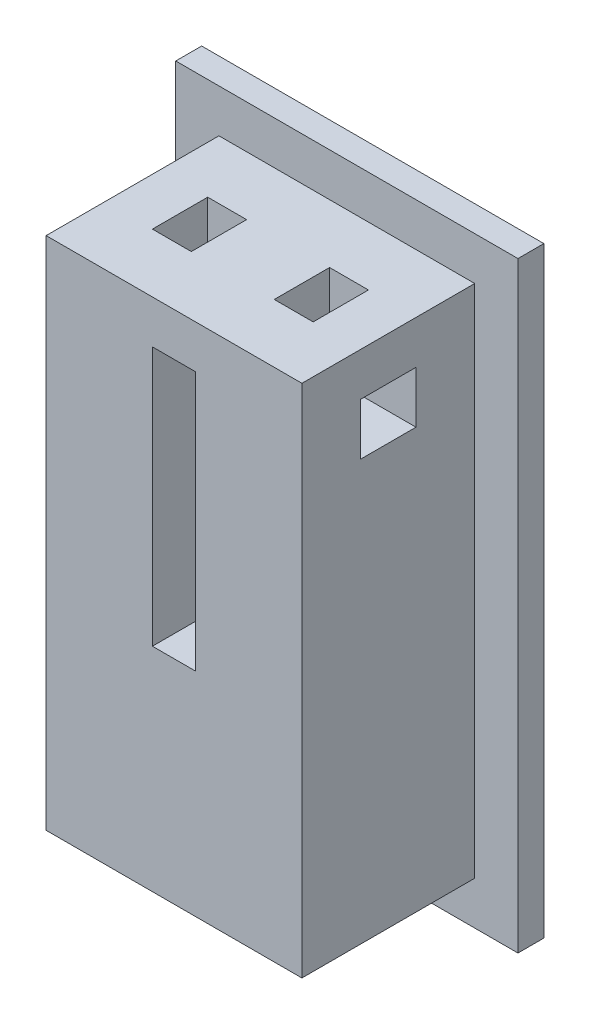
SolidWorks part; units mm, degrees
ref_plane "정면" through (0, 0, 0) normal (0, 0, 1) x (1, 0, 0)
ref_plane "윗면" through (0, 0, 0) normal (0, 1, 0) x (1, 0, 0)
ref_plane "우측면" through (0, 0, 0) normal (1, 0, 0) x (0, 0, -1)
sketch "스케치1" plane through (0, 0, 0) normal (0, 0, 1) x (1, 0, 0)
  line L1 (-2.5, 24.8) -> (2.5, 24.8)
  line L2 (-2.5, 24.8) -> (-2.5, -5.2)
  line L3 (-2.5, -5.2) -> (2.5, -5.2)
  line L4 (2.5, 24.8) -> (2.5, -5.2)
  line L5 (-2.5, 24.8) -> (2.5, -5.2) construction
  line L6 (-2.5, -5.2) -> (2.5, 24.8) construction
  line L7 (-14.8, 29.8) -> (14.8, 29.8)
  line L8 (-14.8, 29.8) -> (-14.8, -29.8)
  line L9 (-14.8, -29.8) -> (14.8, -29.8)
  line L10 (14.8, 29.8) -> (14.8, -29.8)
  line L11 (-14.8, 29.8) -> (14.8, -29.8) construction
  line L12 (-14.8, -29.8) -> (14.8, 29.8) construction
  point P4 (0, 0)
  point P9 (0, 0)
  point P22 (0, -5.2)
  point P23 (0, -29.8)
  point P24 (0, 0)
  dimension "D1" = 5
  dimension "D2" = 30
  dimension "D3" = 29.6
  dimension "D4" = 59.6
  dimension "D5" = 5
extrude "보스-돌출1" add sketch "스케치1" along normal blind 20
sketch "스케치2" plane through (0, 0, 0) normal (0, 0, -1) x (-1, 0, 0)
  line L0 (-14.8, 29.8) -> (14.8, 29.8) construction
  line L1 (-19.8, 34.8) -> (19.8, 34.8)
  line L2 (-19.8, 34.8) -> (-19.8, -34.8)
  line L3 (-19.8, -34.8) -> (19.8, -34.8)
  line L4 (19.8, 34.8) -> (19.8, -34.8)
  line L5 (-19.8, 34.8) -> (19.8, -34.8) construction
  line L6 (-19.8, -34.8) -> (19.8, 34.8) construction
  line L7 (-2.5, 24.8) -> (2.5, 24.8)
  line L8 (-2.5, 24.8) -> (-2.5, -5.2)
  line L9 (-2.5, -5.2) -> (2.5, -5.2)
  line L10 (2.5, 24.8) -> (2.5, -5.2)
  line L11 (-2.5, 24.8) -> (2.5, -5.2) construction
  line L12 (-2.5, -5.2) -> (2.5, 24.8) construction
  line L13 (14.8, 29.8) -> (14.8, -29.8) construction
  point P4 (0, 0)
  point P11 (0, 9.8)
  dimension "D1" = 5
  dimension "D2" = 5
extrude "보스-돌출2" add sketch "스케치2" along normal blind 3
sketch "스케치3" plane through (0, 29.8, 0) normal (0, 1, 0) x (1, 0, 0)
  line L1 (-9.3, -6.8) -> (-4.8, -6.8)
  line L2 (-9.3, -6.8) -> (-9.3, -13.2)
  line L3 (-9.3, -13.2) -> (-4.8, -13.2)
  line L4 (-4.8, -6.8) -> (-4.8, -13.2)
  line L5 (-9.3, -6.8) -> (-4.8, -13.2) construction
  line L6 (-9.3, -13.2) -> (-4.8, -6.8) construction
  line L8 (0, 0) -> (0, -20) construction
  line L9 (14.8, 0) -> (-14.8, 0) construction
  line L10 (14.8, -20) -> (-14.8, -20) construction
  line L12 (9.3, -13.2) -> (4.8, -13.2)
  line L13 (4.8, -6.8) -> (4.8, -13.2)
  line L14 (9.3, -6.8) -> (4.8, -6.8)
  line L15 (9.3, -6.8) -> (9.3, -13.2)
  point P4 (-7.05, -10)
  point P8 (0, -10)
  dimension "D1" = 6.4
  dimension "D2" = 4.8
  dimension "D3" = 4.5
extrude "컷-돌출1" cut sketch "스케치3" against normal blind 11
ref_plane "평면1" through (0, 18.8, 0) normal (0, 1, 0) x (1, 0, 0)
sketch "스케치5" plane through (-14.8, 0, 0) normal (-1, 0, 0) x (0, 0, 1)
  line L1 (6.8, 18.8) -> (13.2, 18.8)
  line L2 (6.8, 18.8) -> (6.8, 24.8)
  line L3 (6.8, 24.8) -> (13.2, 24.8)
  line L4 (13.2, 18.8) -> (13.2, 24.8)
  line L5 (6.8, 18.8) -> (13.2, 24.8) construction
  line L6 (6.8, 24.8) -> (13.2, 18.8) construction
  line L8 (6.8, 29.8) -> (13.2, 29.8) construction
  line L9 (2.475, 18.8) -> (-2.475, 18.8) construction
  line L10 (20, 24.8) -> (-3, 24.8) construction
  line L12 (13.2, 29.8) -> (6.8, 29.8) construction
  point P4 (10, 21.8)
  point P13 (10, 29.8)
extrude "컷-돌출2" cut sketch "스케치5" against normal through all
